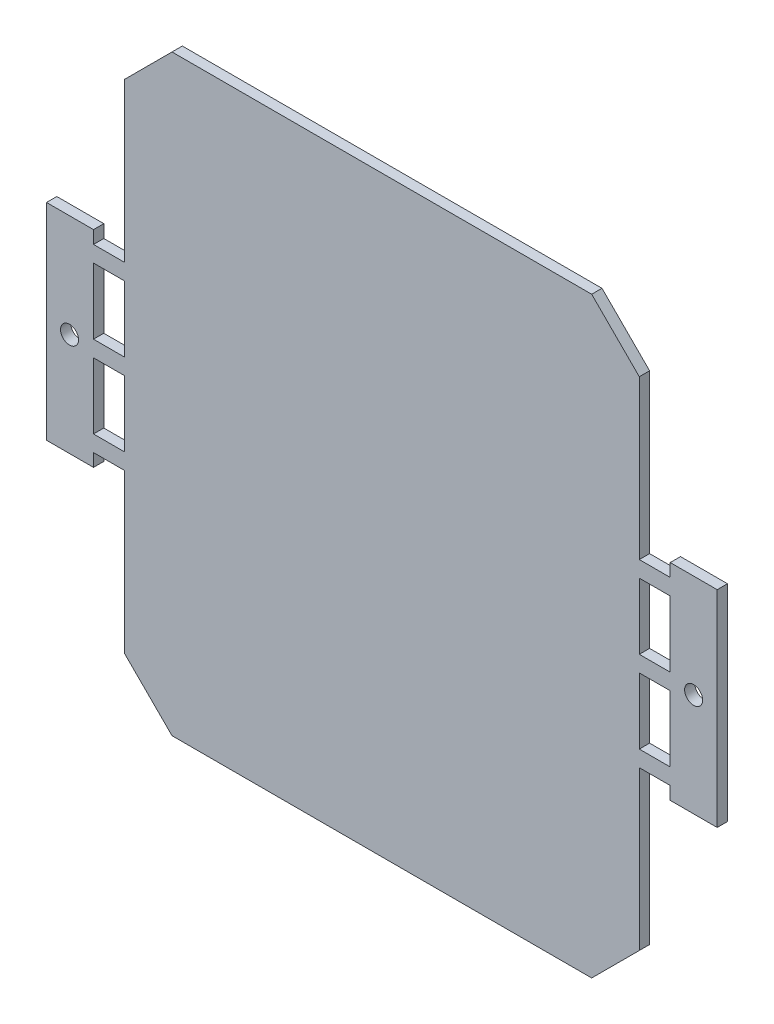
SolidWorks part; units mm, degrees
ref_plane "Płaszczyzna przednia" through (0, 0, 0) normal (0, 0, 1) x (1, 0, 0)
ref_plane "Płaszczyzna górna" through (0, 0, 0) normal (0, 1, 0) x (1, 0, 0)
ref_plane "Płaszczyzna prawa" through (0, 0, 0) normal (1, 0, 0) x (0, 0, -1)
sketch "Sketch1" plane through (0, 0, 0) normal (0, 0, 1) x (1, 0, 0)
  line L0 (0, 30) -> (2.4, 30)
  line L1 (-3.7, 0) -> (-36.3, 0)
  line L2 (0, 3.7) -> (0, 16)
  line L3 (-3.7, 46) -> (-36.3, 46)
  line L4 (-40, 3.7) -> (-40, 16)
  line L5 (0, 0) -> (-40, 46) construction
  line L6 (0, 46) -> (-40, 0) construction
  line L7 (2.4, 30) -> (2.4, 31)
  line L8 (2.4, 31) -> (6.05, 31)
  line L9 (6.05, 31) -> (6.05, 15)
  line L10 (6.05, 15) -> (2.4, 15)
  line L11 (2.4, 15) -> (2.4, 16)
  line L12 (2.4, 16) -> (0, 16)
  line L14 (0, 17.25) -> (2.4, 17.25)
  line L15 (2.4, 17.25) -> (2.4, 22.375)
  line L16 (2.4, 22.375) -> (0, 22.375)
  line L18 (0, 23.625) -> (2.4, 23.625)
  line L19 (2.4, 23.625) -> (2.4, 28.75)
  line L20 (2.4, 28.75) -> (0, 28.75)
  line L22 (-20, 46) -> (-20, 0) construction
  line L23 (-42.4, 28.75) -> (-40, 28.75)
  line L24 (-42.4, 23.625) -> (-42.4, 28.75)
  line L25 (-40, 23.625) -> (-42.4, 23.625)
  line L27 (-42.4, 22.375) -> (-40, 22.375)
  line L28 (-42.4, 17.25) -> (-42.4, 22.375)
  line L29 (-40, 17.25) -> (-42.4, 17.25)
  line L31 (-42.4, 16) -> (-40, 16)
  line L32 (-42.4, 15) -> (-42.4, 16)
  line L33 (-46.05, 15) -> (-42.4, 15)
  line L34 (-46.05, 31) -> (-46.05, 15)
  line L35 (-42.4, 31) -> (-46.05, 31)
  line L36 (-42.4, 30) -> (-42.4, 31)
  line L37 (-40, 30) -> (-42.4, 30)
  line L39 (0, 30) -> (0, 42.3)
  line L40 (0, 23.625) -> (0, 28.75)
  line L41 (0, 17.25) -> (0, 22.375)
  line L42 (-40, 30) -> (-40, 42.3)
  line L43 (-40, 23.625) -> (-40, 28.75)
  line L44 (-40, 17.25) -> (-40, 22.375)
  line L45 (-36.3, 0) -> (-40, 3.7)
  line L46 (0, 3.7) -> (-3.7, 0)
  line L47 (-36.3, 46) -> (-40, 42.3)
  line L48 (0, 42.3) -> (-3.7, 46)
  circle A0 centre (4.2181, 23) radius 0.7
  circle A1 centre (-44.2626, 23) radius 0.7
  point P4 (-20, 23)
  dimension "D16" = 1.4
  dimension "D18" = 1.4
  dimension "D1" = 46
  dimension "D2" = 40
  dimension "D3" = 16
  dimension "D4" = 3.65
  dimension "D5" = 3.65
  dimension "D6" = 3.65
  dimension "D7" = 2.4
  dimension "D8" = 1.25
  dimension "D9" = 1.25
  dimension "D10" = 1.25
  dimension "D11" = 1
  dimension "D12" = 1
  dimension "D13" = 5.125
  dimension "D14" = 5.125
  dimension "D15" = 15
  dimension "D17" = 8
extrude "Boss-Extrude1" add sketch "Sketch1" along normal blind 0.8
